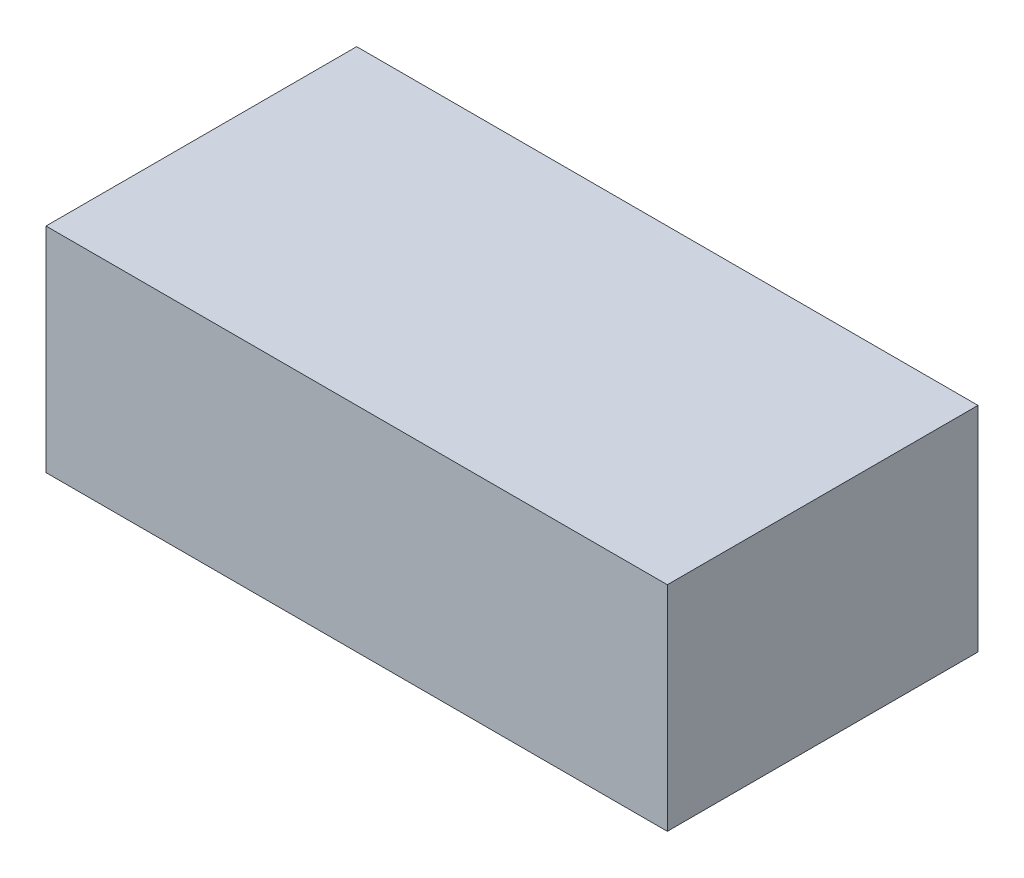
SolidWorks part; units mm, degrees
material "PC High Viscosity"
ref_plane "Front Plane" through (0, 0, 0) normal (0, 0, 1) x (1, 0, 0)
ref_plane "Top Plane" through (0, 0, 0) normal (0, 1, 0) x (1, 0, 0)
ref_plane "Right Plane" through (0, 0, 0) normal (1, 0, 0) x (0, 0, -1)
sketch "BaseS" plane through (0, 0, 0) normal (0, 1, 0) x (1, 0, 0)
  line L1 (-0.8, 0.4) -> (0.8, 0.4)
  line L2 (-0.8, 0.4) -> (-0.8, -0.4)
  line L3 (-0.8, -0.4) -> (0.8, -0.4)
  line L4 (0.8, 0.4) -> (0.8, -0.4)
  line L5 (-0.8, 0.4) -> (0.8, -0.4) construction
  line L6 (-0.8, -0.4) -> (0.8, 0.4) construction
  point P0 (0, 0)
  dimension "Width" = 1.6
  dimension "Length" = 0.8
extrude "Base" add sketch "BaseS" along normal blind 0.55
